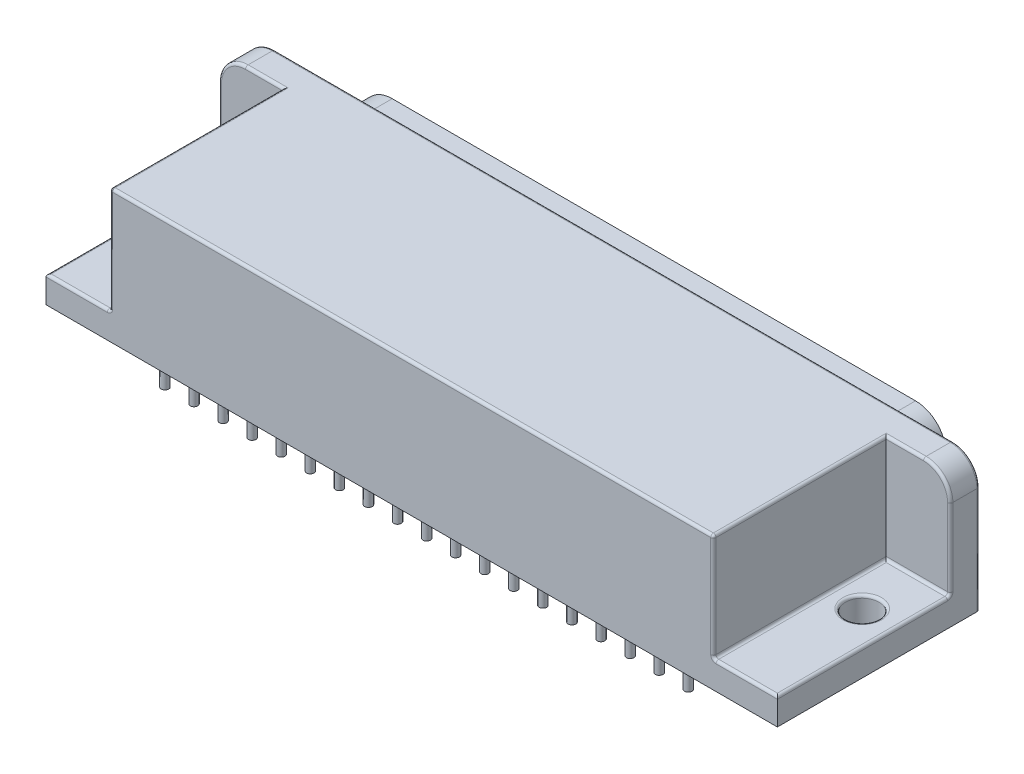
SolidWorks part; units mm, degrees
ref_plane "Front Plane" through (0, 0, 0) normal (0, 0, 1) x (1, 0, 0)
ref_plane "Top Plane" through (0, 0, 0) normal (0, 1, 0) x (1, 0, 0)
ref_plane "Right Plane" through (0, 0, 0) normal (1, 0, 0) x (0, 0, -1)
sketch "Sketch1" plane through (0, 0, 0) normal (0, 1, 0) x (1, 0, 0)
  line L1 (-9.906, -1.4224) -> (59.7408, -1.4224)
  line L2 (-9.906, -1.4224) -> (-9.906, 17.8308)
  line L3 (-9.906, 17.8308) -> (59.7408, 17.8308)
  line L4 (59.7408, -1.4224) -> (59.7408, 17.8308)
  point P3 (24.9174, 17.8308)
  dimension "D1" = 69.6468
  dimension "D2" = 19.2532
  dimension "D3" = 1.4224
  dimension "D4" = 9.906
extrude "Base-Extrude" add sketch "Sketch1" along normal blind 12.7
sketch "Sketch2" plane through (0, 0, -17.8308) normal (0, 0, -1) x (-1, 0, 0)
  line L0 (-24.9174, 12.7) -> (-24.9174, -6.5379) construction
  line L1 (-59.7408, 12.7) -> (9.906, 12.7) construction
  line L2 (-49.3393, 2.032) -> (-0.4955, 2.032)
  line L3 (2.3614, 4.3892) -> (2.8571, 6.9513)
  line L4 (0.0002, 10.414) -> (-49.835, 10.414)
  line L5 (-59.7408, 0) -> (9.906, 0) construction
  line L6 (-52.1962, 4.3892) -> (-52.6919, 6.9513)
  arc A0 (2.3614, 4.3892) -> (-0.4955, 2.032) centre (-0.4955, 4.9419) cw
  arc A1 (0.0002, 10.414) -> (2.8571, 6.9513) centre (0.0002, 7.5041) cw
  arc A2 (-49.835, 10.414) -> (-52.6919, 6.9513) centre (-49.835, 7.5041) ccw
  arc A3 (-52.1962, 4.3892) -> (-49.3393, 2.032) centre (-49.3393, 4.9419) ccw
  point P4 (-24.9174, 10.414)
  point P12 (1.9054, 2.032)
  point P21 (-24.9174, 2.032)
  dimension "D1" = 2.032
  dimension "D2" = 8.382
  dimension "D3" = 100.95
  dimension "D4" = 48.8437
  dimension "D6" = 49.8351
extrude "Boss-Extrude1" add sketch "Sketch2" along normal blind 3.81
sketch "Sketch13" plane through (0, 0, -21.6408) normal (0, 0, -1) x (-1, 0, 0)
  line L8 (2.112, 4.4374) -> (2.6077, 6.9996)
  line L9 (0.0002, 10.16) -> (-49.835, 10.16)
  line L10 (-52.4425, 6.9996) -> (-51.9468, 4.4374)
  line L11 (-49.3393, 2.286) -> (-0.4955, 2.286)
  line L12 (2.112, 4.4374) -> (2.6077, 6.9996)
  line L13 (0.0002, 10.16) -> (-49.835, 10.16)
  line L14 (-52.4425, 6.9996) -> (-51.9468, 4.4374)
  line L15 (-49.3393, 2.286) -> (-0.4955, 2.286)
  arc A8 (-0.4955, 2.286) -> (2.112, 4.4374) centre (-0.4955, 4.9419) ccw
  arc A9 (2.6077, 6.9996) -> (0.0002, 10.16) centre (0.0002, 7.5041) ccw
  arc A10 (-49.835, 10.16) -> (-52.4425, 6.9996) centre (-49.835, 7.5041) ccw
  arc A11 (-51.9468, 4.4374) -> (-49.3393, 2.286) centre (-49.3393, 4.9419) ccw
  arc A12 (-0.4955, 2.286) -> (2.112, 4.4374) centre (-0.4955, 4.9419) ccw
  arc A13 (2.6077, 6.9996) -> (0.0002, 10.16) centre (0.0002, 7.5041) ccw
  arc A14 (-49.835, 10.16) -> (-52.4425, 6.9996) centre (-49.835, 7.5041) ccw
  arc A15 (-51.9468, 4.4374) -> (-49.3393, 2.286) centre (-49.3393, 4.9419) ccw
  dimension "D1" = 0.254
extrude "Cut-Extrude5" cut sketch "Sketch13" against normal blind 3.81
sketch "Sketch4" plane through (0, 0, -17.8308) normal (0, 0, -1) x (-1, 0, 0)
  line L0 (9.906, 12.7) -> (9.906, 0) construction
  line L2 (-59.7408, 12.7) -> (9.906, 12.7) construction
  circle A0 centre (-0.254, 7.62) radius 0.508
  dimension "D1" = 1.016
  dimension "D2" = 10.16
  dimension "D3" = 5.08
extrude "Boss-Extrude4" add sketch "Sketch4" along normal blind 3.81
fillet "Fillet7" radius 0.4826 1 edges at (-0.254, 7.62, -21.6408)
pattern_linear "LPattern5" count 19 spacing 2.7686 along (1, 0, 0) of "Boss-Extrude4", "Fillet7"
sketch "Sketch5" plane through (0, 0, -17.8308) normal (0, 0, -1) x (-1, 0, 0)
  line L0 (9.906, 12.7) -> (9.906, 0) construction
  line L2 (-59.7408, 0) -> (9.906, 0) construction
  circle A0 centre (-1.651, 5.08) radius 0.508
  circle A2 centre (-0.254, 7.62) radius 0.508 construction
  dimension "D2" = 5.08
  dimension "D1" = 11.557
extrude "Boss-Extrude6" add sketch "Sketch5" along normal blind 3.81
fillet "Fillet8" radius 0.4826 1 edges at (1.143, 5.08, -21.6408)
pattern_linear "LPattern6" count 18 spacing 2.7686 along (1, 0, 0) of "Fillet8", "Boss-Extrude6"
sketch "Sketch6" plane through (0, 0, 0) normal (0, -1, 0) x (1, 0, 0)
  circle A0 centre (0, 0) radius 0.3556
  dimension "D1" = 0.7112
extrude "Boss-Extrude2" add sketch "Sketch6" along normal blind 2.54
pattern_linear "LPattern1" count 19 spacing 2.7686 along (1, 0, 0) of "Boss-Extrude2"
sketch "Sketch7" plane through (0, 0, 0) normal (0, -1, 0) x (1, 0, 0)
  line L1 (-9.906, -17.8308) -> (-9.906, 1.4224) construction
  circle A0 centre (1.651, -2.54) radius 0.3556
  dimension "D1" = 0.7112
  dimension "D2" = 11.557
  dimension "D3" = 2.54
extrude "Boss-Extrude3" add sketch "Sketch7" along normal up to surface (2.54 mm away) up to face at (0, -2.54, -0.3556)
pattern_linear "LPattern4" count 18 spacing 2.7686 along (1, 0, 0) of "Boss-Extrude3"
ref_plane "Mid Plane" through (24.9174, 0, 0) normal (1, 0, 0) x (0, 0, -1)
sketch "Sketch9" plane through (0, 0, 1.4224) normal (0, 0, 1) x (1, 0, 0)
  line L1 (-9.906, 12.7) -> (-3.81, 12.7)
  line L2 (-9.906, 12.7) -> (-9.906, 2.54)
  line L3 (-9.906, 2.54) -> (-3.81, 2.54)
  line L4 (-3.81, 12.7) -> (-3.81, 2.54)
  dimension "D1" = 10.16
  dimension "D2" = 6.096
extrude "Cut-Extrude3" cut sketch "Sketch9" against normal blind 16.4592
sketch "Sketch11" plane through (0, 2.54, 0) normal (0, 1, 0) x (-1, 0, 0)
  line L0 (9.906, 1.4224) -> (3.81, 1.4224) construction
  line L1 (9.906, -15.0368) -> (9.906, 1.4224) construction
  circle A0 centre (6.731, -9.8298) radius 1.5875
  point P2 (6.858, 1.4224)
  dimension "D1" = 3.175
  dimension "D2" = 11.2522
  dimension "D3" = 3.175
extrude "Cut-Extrude4" cut sketch "Sketch11" against normal through all
mirror "Mirror1" about plane through (24.9174, 0, 0) normal (1, 0, 0) of "Cut-Extrude4", "Cut-Extrude3"
fillet "Fillet1" radius 2.54 2 edges at (-9.906, 12.7, -16.4338) (59.7408, 7.62, -15.0368)
fillet "Fillet2" radius 0.254 26 edges at (24.9174, 12.7, 1.4224) (-9.906, 2.54, -6.8072) (-5.588, 12.7, -15.0368) (-3.81, 12.7, -6.8072) (-6.858, 2.54, -15.0368) (-3.81, 2.54, -6.8072) (-6.858, 2.54, 1.4224) (-3.81, 7.62, 1.4224) (-6.731, 2.54, -8.2423) (56.6928, 2.54, 1.4224) (59.7408, 2.54, -6.8072) (53.6448, 7.62, 1.4224) (53.6448, 2.54, -6.8072) (53.6448, 12.7, -6.8072) (56.6928, 2.54, -15.0368) (55.4228, 12.7, -15.0368) (56.5658, 2.54, -8.2423) (24.9174, 12.7, -17.8308) (-9.906, 6.35, -15.0368) (-9.1621, 11.9561, -15.0368) (-9.906, 5.08, -17.8308) (59.7408, 5.08, -17.8308) (58.9969, 11.9561, -17.8308) (-9.1621, 11.9561, -17.8308) (59.7408, 6.35, -15.0368) (58.9969, 11.9561, -15.0368)
sketch "Component_Outline" plane through (0, 0, 0) normal (0, -1, 0) x (1, 0, 0)
  line L0 (49.3393, -21.6408) -> (0.4955, -21.6408) construction
  line L1 (-9.906, 1.4224) -> (59.7408, 1.4224)
  line L2 (-9.906, 1.4224) -> (-9.906, -21.6408)
  line L3 (-9.906, -21.6408) -> (59.7408, -21.6408)
  line L4 (59.7408, 1.4224) -> (59.7408, -21.6408)
  line L5 (59.7408, 1.4224) -> (59.7408, -17.5768) construction
